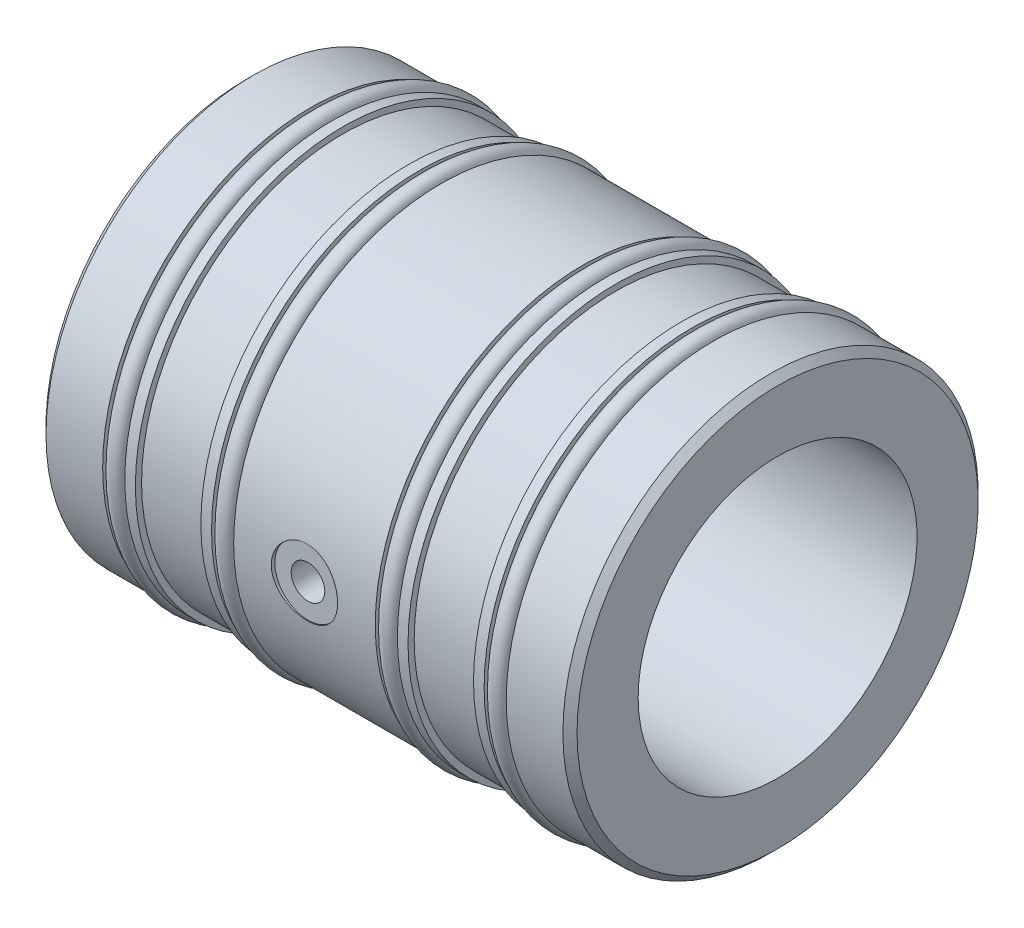
SolidWorks part; units mm, degrees
ref_plane "Front Plane" through (0, 0, 0) normal (0, 0, 1) x (1, 0, 0)
ref_plane "Top Plane" through (0, 0, 0) normal (0, 1, 0) x (1, 0, 0)
ref_plane "Right Plane" through (0, 0, 0) normal (1, 0, 0) x (0, 0, -1)
sketch "Sketch1" plane through (0, 0, 0) normal (0, 0, 1) x (1, 0, 0)
  line L0 (0, 20.01) -> (76.2, 20.01)
  line L1 (76.2, 20.01) -> (76.2, 29.7942)
  line L2 (76.2, 29.7942) -> (67.055, 29.7942)
  line L3 (67.055, 29.7942) -> (67.055, 27.813)
  line L4 (67.055, 27.813) -> (63.88, 27.813)
  line L5 (63.88, 27.813) -> (63.88, 29.7942)
  line L6 (63.88, 29.7942) -> (62.358, 29.7942)
  line L7 (62.358, 29.7942) -> (62.358, 28.905)
  line L8 (0, 20.01) -> (0, 29.7942)
  line L9 (0, 29.7942) -> (9.144, 29.7942)
  line L10 (9.144, 29.7942) -> (9.144, 27.813)
  line L11 (9.144, 27.813) -> (12.319, 27.813)
  line L12 (12.319, 27.813) -> (12.319, 29.7942)
  line L13 (12.319, 29.7942) -> (13.84, 29.7942)
  line L14 (13.84, 29.7942) -> (13.84, 28.905)
  line L15 (13.84, 28.905) -> (23.238, 28.905)
  line L16 (23.238, 28.905) -> (23.238, 29.7942)
  line L17 (23.238, 29.7942) -> (24.77, 29.7942)
  line L18 (24.77, 29.7942) -> (24.77, 27.813)
  line L19 (24.77, 27.813) -> (27.945, 27.813)
  line L20 (27.945, 27.813) -> (27.945, 29.7942)
  line L21 (27.945, 29.7942) -> (48.26, 29.7942)
  line L22 (48.26, 29.7942) -> (48.26, 27.813)
  line L23 (62.358, 28.905) -> (52.96, 28.905)
  line L24 (52.96, 28.905) -> (52.96, 29.7942)
  line L25 (52.96, 29.7942) -> (51.435, 29.7942)
  line L26 (51.435, 29.7942) -> (51.435, 27.813)
  line L27 (51.435, 27.813) -> (48.26, 27.813)
  line L28 (0, 0) -> (76.2, 0) construction
  dimension "D1" = 27.813
  dimension "Bore ID" = 40.02
  dimension "D2" = 20.01
  dimension "OAL" = 76.2
  dimension "Moglice groove width" = 9.398
  dimension "O-ring groove width" = 3.175
  dimension "Edge to 1st o-ring groove" = 9.144
  dimension "Edge to 2nd o-ring groove" = 24.77
  dimension "Bushing OD" = 59.5884
  dimension "O-ring groove dia" = 55.626
  dimension "Edge to 3rd o-ring groove" = 48.26
  dimension "edge to 4th o-ring groove" = 63.88
  dimension "Edge to 1st moglice groove" = 13.84
  dimension "Edge to 2nd moglice groove" = 52.96
  dimension "Moglice Groove Dia" = 57.81
revolve "Revolve1" add sketch "Sketch1" angle 360 about L28
chamfer "Chamfer1" distance 1.016 angle 45 2 edges at (0, 0, 29.7942) (76.2, 0, 29.7942)
ref_plane "Plane1" through (0, 0, -7.9121) normal (0, 0, 1) x (1, 0, 0)
hole_wizard "3/8 (0.375) Diameter Hole1" positions "3DSketch1" profile "Sketch2" hole size "3/8" standard "Ansi Inch"
sketch3d "3DSketch1"
  point P0 (38.1, 0, 29.7942)
  dimension "Edge to air hole" = 38.1
sketch "Sketch2" plane through (38.1, 0, 29.7942) normal (1, 0, 0) x (0, -1, 0)
  line L0 (0, 0) -> (0, 0.51)
  line L1 (0, 0.51) -> (4.7625, 0.51)
  line L2 (4.7625, 0.51) -> (4.7625, 0)
  line L5 (4.7625, 0) -> (0, 0)
  line L10 (0, 0.51) -> (-4.7625, 0.51) construction
  line L11 (0, -6.35) -> (0, 107.95) construction
  dimension "Hole Dia." = 9.525
  dimension "Hole Depth" = 0.51
  dimension "Drill Angle" = 180
hole_wizard "Air Hole" positions "Sketch4" profile "Sketch3" tap size "M3x0.5" standard "Ansi Metric"
sketch "Sketch4" plane through (0, 0, 29.2842) normal (0, 0, 1) x (1, 0, 0)
  circle A0 centre (38.1, 0) radius 4.7625 construction
  point P0 (38.1, 0)
sketch "Sketch3" plane through (38.1, 0, 29.2842) normal (1, 0, 0) x (0, -1, 0)
  line L0 (0, 0) -> (0, 7.5786)
  line L1 (0, 7.5786) -> (2.0447, 6.35)
  line L2 (2.0447, 6.35) -> (2.0447, 5.994)
  line L3 (2.0447, 5.994) -> (2.413, 5.994)
  line L4 (2.413, 5.994) -> (2.413, 0)
  line L5 (2.413, 0) -> (0, 0)
  line L10 (0, 7.5786) -> (-2.0447, 6.35) construction
  line L11 (0, -6.35) -> (0, 107.95) construction
  dimension "Tap Drill Dia." = 4.0894
  dimension "Tap Drill Depth" = 6.35
  dimension "Thread Major Dia." = 4.826
  dimension "Thread Depth" = 5.994
  dimension "Drill Angle" = 118
sketch "Sketch5" plane through (0, 0, 0) normal (0, 0, 1) x (1, 0, 0)
  line L3 (12.319, 29.7942) -> (12.319, -29.7942) construction
  line L4 (27.945, 29.7942) -> (27.945, -29.7942) construction
  line L5 (48.26, -29.7942) -> (48.26, 29.7942) construction
  line L6 (63.88, -29.7942) -> (63.88, 29.7942) construction
  line L7 (0, 0) -> (51.7691, 0) construction
  circle A0 centre (65.4675, 29.0957) radius 1.2827
  circle A1 centre (49.8475, 29.0957) radius 1.2827
  circle A2 centre (26.3575, 29.0957) radius 1.2827
  circle A3 centre (10.7315, 29.0957) radius 1.2827
  dimension "D1" = 2.5654
  dimension "D2" = 30.3784
  dimension "D6" = 1.5875
  dimension "D3" = 1.5875
  dimension "D4" = 1.5875
  dimension "D5" = 1.5875
revolve "Revolve2" add sketch "Sketch5" angle 360 about L7
equation "\"plane offset\"= \"Bushing OD@Sketch1\" / 2"
